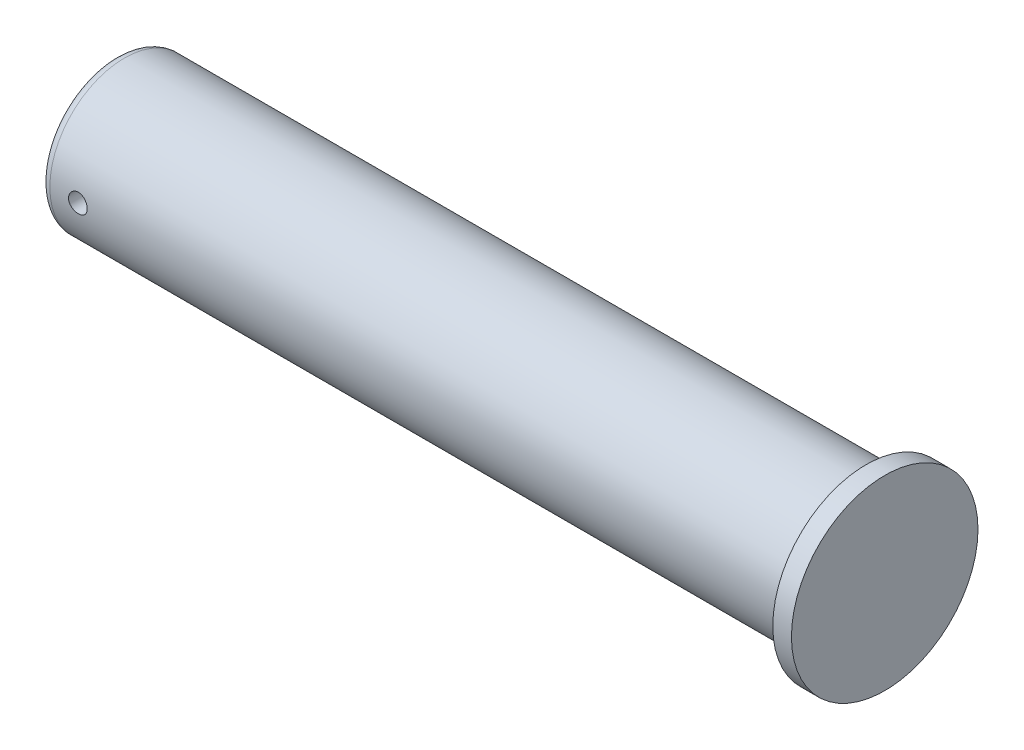
SolidWorks part; units mm, degrees
ref_plane "Ebene vorne" through (0, 0, 0) normal (0, 0, 1) x (1, 0, 0)
ref_plane "Ebene oben" through (0, 0, 0) normal (0, 1, 0) x (1, 0, 0)
ref_plane "Ebene rechts" through (0, 0, 0) normal (1, 0, 0) x (0, 0, -1)
sketch "Skizze1" plane through (0, 0, 0) normal (0, 0, 1) x (1, 0, 0)
  line L0 (0, 0) -> (0, 8)
  line L1 (0, 8) -> (80.5, 8)
  line L2 (80.5, 8) -> (80.5, 10)
  line L3 (80.5, 10) -> (82.5, 10)
  line L4 (82.5, 10) -> (82.5, 0)
  line L5 (82.5, 0) -> (0, 0)
  line L6 (-15.9566, 0) -> (57.6328, 0) construction
  dimension "D1" = 16
  dimension "D2" = 20
  dimension "D3" = 2
  dimension "D4" = 82.5
revolve "Rotation1" add sketch "Skizze1" angle 360 about L6
sketch "Skizze2" plane through (0, 0, 0) normal (0, 0, 1) x (1, 0, 0)
  line L0 (11, 0) -> (-11, 0) construction
  line L1 (0, -11) -> (0, 11) construction
  circle A0 centre (4, 0) radius 1
  dimension "D1" = 2
  dimension "D2" = 4
extrude "Schnitt-Linear austragen1" cut sketch "Skizze2" against normal up to next and the other way through all
fillet "Verrundung1" radius 1 1 edges at (0, 0, 8)
